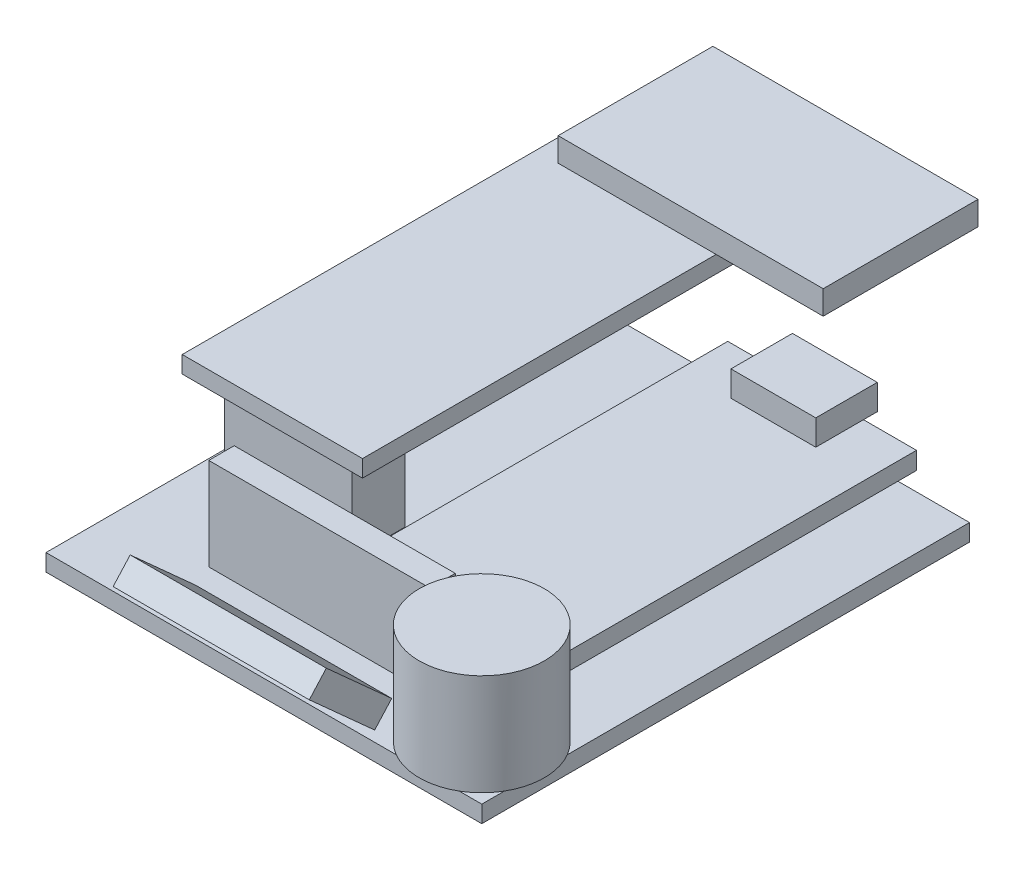
SolidWorks part; units mm, degrees
ref_plane "Front Plane" through (0, 0, 0) normal (0, 0, 1) x (1, 0, 0)
ref_plane "Top Plane" through (0, 0, 0) normal (0, 1, 0) x (1, 0, 0)
ref_plane "Right Plane" through (0, 0, 0) normal (1, 0, 0) x (0, 0, -1)
sketch "Sketch1" plane through (0, 0, 0) normal (0, 1, 0) x (1, 0, 0)
  line L1 (-9.0024, 19.489) -> (32.0976, 19.489)
  line L2 (-9.0024, 19.489) -> (-9.0024, -26.511)
  line L3 (-9.0024, -26.511) -> (32.0976, -26.511)
  line L4 (32.0976, 19.489) -> (32.0976, -26.511)
  dimension "D1" = 46
  dimension "D2" = 41.1
extrude "Boss-Extrude1" add sketch "Sketch1" along normal blind 1.6
sketch "Sketch2" plane through (0, 1.6, 0) normal (0, 1, 0) x (1, 0, 0)
  line L0 (32.0976, -26.511) -> (32.0976, 19.489) construction
  line L1 (-9.0024, -26.511) -> (32.0976, -26.511) construction
  circle A0 centre (26.9976, -21.411) radius 5.9
  dimension "D1" = 11.8
  dimension "D2" = 5.1
  dimension "D3" = 5.1
extrude "Boss-Extrude2" add sketch "Sketch2" along normal blind 9.55
sketch "Sketch3" plane through (0, 1.6, 0) normal (0, 1, 0) x (1, 0, 0)
  line L0 (32.0976, -18.4445) -> (32.0976, 19.489) construction
  line L1 (10.2976, 18.489) -> (28.0976, 18.489)
  line L2 (10.2976, 18.489) -> (10.2976, -14.611)
  line L3 (10.2976, -14.611) -> (28.0976, -14.611)
  line L4 (28.0976, 18.489) -> (28.0976, -14.611)
  line L5 (32.0976, 19.489) -> (-9.0024, 19.489) construction
  dimension "D1" = 17.8
  dimension "D2" = 33.1
  dimension "D3" = 4
  dimension "D4" = 1
extrude "Boss-Extrude3" add sketch "Sketch3" along normal blind 1.65 from offset 2.75 separate body
sketch "Sketch4" plane through (0, 6, 0) normal (0, 1, 0) x (1, 0, 0)
  line L0 (28.0976, 18.489) -> (10.2976, 18.489) construction
  line L1 (15.0976, 13.989) -> (23.0976, 13.989)
  line L2 (15.0976, 13.989) -> (15.0976, 19.789)
  line L3 (15.0976, 19.789) -> (23.0976, 19.789)
  line L4 (23.0976, 13.989) -> (23.0976, 19.789)
  line L5 (28.0976, -14.611) -> (28.0976, 18.489) construction
  dimension "D1" = 8
  dimension "D2" = 5.8
  dimension "D3" = 1.3
  dimension "D4" = 5
extrude "Boss-Extrude4" add sketch "Sketch4" along normal blind 2.4
sketch "Sketch5" plane through (0, 1.6, 0) normal (0, 1, 0) x (1, 0, 0)
  line L0 (-9.0024, -26.511) -> (24.0311, -26.511) construction
  line L1 (-6.1524, -7.511) -> (5.8476, -7.511)
  line L2 (-6.1524, -7.511) -> (-6.1524, -12.511)
  line L3 (-6.1524, -12.511) -> (5.8476, -12.511)
  line L4 (5.8476, -7.511) -> (5.8476, -12.511)
  line L5 (-9.0024, 19.489) -> (-9.0024, -26.511) construction
  dimension "D1" = 12
  dimension "D2" = 5
  dimension "D3" = 14
  dimension "D4" = 2.85
extrude "Boss-Extrude5" add sketch "Sketch5" along normal blind 8.5
sketch "Sketch7" plane through (0, 1.6, 0) normal (0, 1, 0) x (1, 0, 0)
  line L0 (-9.0024, 19.489) -> (-9.0024, -26.511) construction
  line L1 (-0.1524, -17.611) -> (20.6976, -17.611)
  line L2 (-0.1524, -17.611) -> (-0.1524, -20.011)
  line L3 (-0.1524, -20.011) -> (20.6976, -20.011)
  line L4 (20.6976, -17.611) -> (20.6976, -20.011)
  line L5 (-9.0024, -26.511) -> (24.0311, -26.511) construction
  dimension "D1" = 2.4
  dimension "D2" = 20.85
  dimension "D3" = 8.85
  dimension "D4" = 6.5
extrude "Boss-Extrude7" add sketch "Sketch7" along normal blind 8.7
sketch "Sketch8" plane through (-9.0024, 0, 0) normal (-1, 0, 0) x (0, 0, 1)
  line L0 (23.9051, 3.3835) -> (30.0732, 8.9373)
  line L1 (30.0732, 8.9373) -> (31.6791, 7.1538)
  line L2 (31.6791, 7.1538) -> (25.511, 1.6)
  line L3 (25.511, 1.6) -> (23.9051, 3.3835)
  line L4 (-19.489, 1.6) -> (26.511, 1.6) construction
  line L5 (26.511, 1.6) -> (15.511, 1.6) construction
  dimension "D1" = 2.4
  dimension "D2" = 8.3
  dimension "D3" = 1
  dimension "D4" = 42
extrude "Boss-Extrude8" add sketch "Sketch8" against normal blind 18.5 from offset 11.5 separate body offset against normal yes
sketch "Sketch9" plane through (0, 10.1, 0) normal (0, 1, 0) x (1, 0, 0)
  line L0 (-6.1524, -7.511) -> (-6.1524, -12.511) construction
  line L1 (-8.6524, -14.011) -> (8.3476, -14.011)
  line L2 (-8.6524, -14.011) -> (-8.6524, 31.989)
  line L3 (-8.6524, 31.989) -> (8.3476, 31.989)
  line L4 (8.3476, -14.011) -> (8.3476, 31.989)
  line L5 (-6.1524, -12.511) -> (5.8476, -12.511) construction
  dimension "D1" = 17
  dimension "D2" = 46
  dimension "D3" = 2.5
  dimension "D4" = 1.5
extrude "Boss-Extrude10" add sketch "Sketch9" along normal blind 1.6
sketch "Sketch6" plane through (0, 11.7, 0) normal (0, 1, 0) x (1, 0, 0)
  line L1 (-5.8524, 33.239) -> (19.1476, 33.239)
  line L2 (-5.8524, 33.239) -> (-5.8524, 18.639)
  line L3 (-5.8524, 18.639) -> (19.1476, 18.639)
  line L4 (19.1476, 33.239) -> (19.1476, 18.639)
  line L7 (8.3476, 31.989) -> (-8.6524, 31.989) construction
  line L8 (-8.6524, 31.989) -> (-8.6524, -14.011) construction
  dimension "D1" = 25
  dimension "D2" = 14.6
  dimension "D3" = 1.25
  dimension "D4" = 2.8
extrude "Boss-Extrude11" add sketch "Sketch6" along normal blind 2.25 from offset 0.7 separate body
